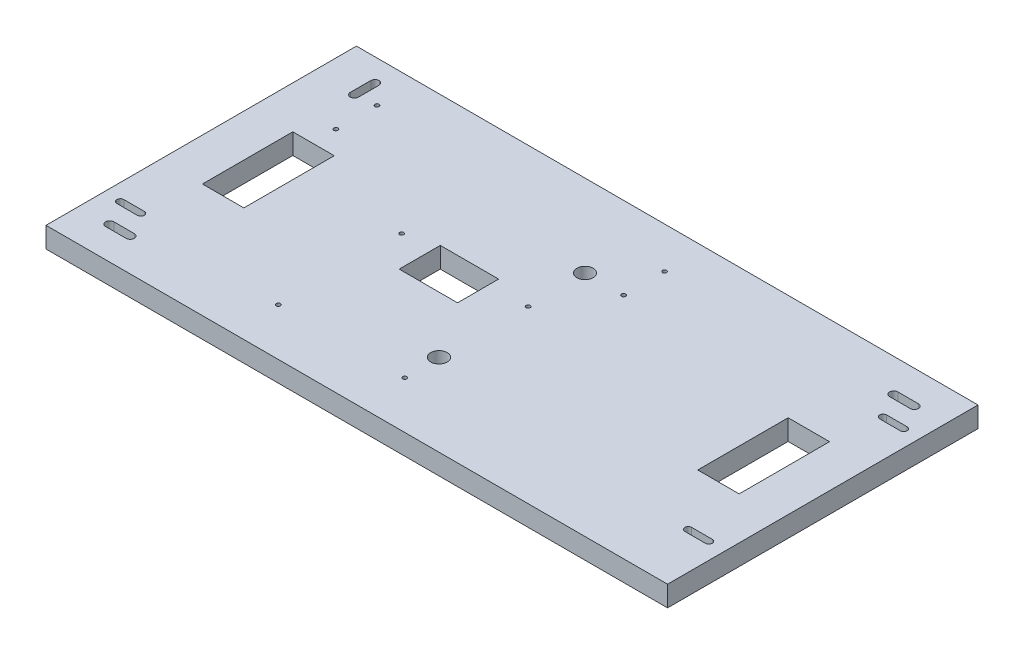
SolidWorks part; units mm, degrees
material "Corrugated Paper"
ref_plane "Front Plane" through (0, 0, 0) normal (0, 0, 1) x (1, 0, 0)
ref_plane "Top Plane" through (0, 0, 0) normal (0, 1, 0) x (1, 0, 0)
ref_plane "Right Plane" through (0, 0, 0) normal (1, 0, 0) x (0, 0, -1)
sketch "Sketch1" plane through (0, 0, 0) normal (0, 1, 0) x (1, 0, 0)
  line L1 (0, 0) -> (192.0875, 0)
  line L2 (0, 0) -> (0, 95.9358)
  line L3 (0, 95.9358) -> (192.0875, 95.9358)
  line L4 (192.0875, 0) -> (192.0875, 95.9358)
  dimension "D1" = 192.0875
  dimension "D2" = 95.9358
extrude "Boss-Extrude1" add sketch "Sketch1" along normal blind 6.35
sketch "Sketch3" plane through (0, 0, 0) normal (0, -1, 0) x (-1, 0, 0)
  line L0 (-12.7, 88.9508) -> (-12.7, 82.6008) construction
  line L1 (-11.43, 88.9508) -> (-11.43, 82.6008)
  line L2 (-13.97, 88.9508) -> (-13.97, 82.6008)
  line L3 (-192.0875, 95.9358) -> (0, 95.9358) construction
  line L4 (-5.1054, 17.8562) -> (-11.4554, 17.8562) construction
  line L5 (0, 95.9358) -> (0, 0) construction
  line L6 (0, 47.9679) -> (-192.0875, 47.9679) construction
  line L7 (-192.0875, 0) -> (-192.0875, 95.9358) construction
  line L8 (-96.0437, 0) -> (-96.0437, 95.9358) construction
  line L9 (0, 0) -> (-192.0875, 0) construction
  line L10 (-182.5625, 85.7758) -> (-176.2125, 85.7758) construction
  line L11 (-182.5625, 84.5058) -> (-176.2125, 84.5058)
  line L12 (-182.5625, 87.0458) -> (-176.2125, 87.0458)
  line L16 (-9.525, 10.16) -> (-15.875, 10.16) construction
  line L17 (-9.525, 11.43) -> (-15.875, 11.43)
  line L18 (-9.525, 8.89) -> (-15.875, 8.89)
  line L19 (-5.1054, 16.7894) -> (-11.4554, 16.7894)
  line L20 (-5.1054, 18.923) -> (-11.4554, 18.923)
  line L21 (-186.9821, 17.8562) -> (-180.6321, 17.8562) construction
  line L22 (-186.9821, 16.7894) -> (-180.6321, 16.7894)
  line L23 (-186.9821, 18.923) -> (-180.6321, 18.923)
  line L24 (-186.9821, 78.0796) -> (-180.6321, 78.0796) construction
  line L25 (-178.9811, 35.2298) -> (-178.9811, 63.1698)
  line L26 (-13.1064, 35.2298) -> (-25.908, 35.2298)
  line L27 (-13.1064, 35.2298) -> (-13.1064, 63.1698)
  line L28 (-13.1064, 63.1698) -> (-25.908, 63.1698)
  line L29 (-25.908, 35.2298) -> (-25.908, 63.1698)
  line L30 (-178.9811, 35.2298) -> (-166.1795, 35.2298)
  line L31 (-166.1795, 35.2298) -> (-166.1795, 63.1698)
  line L32 (-178.9811, 63.1698) -> (-166.1795, 63.1698)
  line L33 (-186.9821, 79.1464) -> (-180.6321, 79.1464)
  line L34 (-66.294, 42.8498) -> (-84.328, 42.8498)
  line L35 (-66.294, 42.8498) -> (-66.294, 55.5498)
  line L36 (-66.294, 55.5498) -> (-84.328, 55.5498)
  line L37 (-84.328, 42.8498) -> (-84.328, 55.5498)
  line L38 (-186.9821, 77.0128) -> (-180.6321, 77.0128)
  arc A0 (-11.43, 88.9508) -> (-13.97, 88.9508) centre (-12.7, 88.9508) ccw
  arc A1 (-13.97, 82.6008) -> (-11.43, 82.6008) centre (-12.7, 82.6008) ccw
  arc A2 (-182.5625, 84.5058) -> (-182.5625, 87.0458) centre (-182.5625, 85.7758) cw
  arc A3 (-176.2125, 87.0458) -> (-176.2125, 84.5058) centre (-176.2125, 85.7758) cw
  arc A6 (-9.525, 11.43) -> (-9.525, 8.89) centre (-9.525, 10.16) cw
  arc A7 (-15.875, 8.89) -> (-15.875, 11.43) centre (-15.875, 10.16) cw
  arc A8 (-5.1054, 16.7894) -> (-5.1054, 18.923) centre (-5.1054, 17.8562) ccw
  arc A9 (-11.4554, 18.923) -> (-11.4554, 16.7894) centre (-11.4554, 17.8562) ccw
  arc A10 (-186.9821, 16.7894) -> (-186.9821, 18.923) centre (-186.9821, 17.8562) cw
  arc A11 (-180.6321, 18.923) -> (-180.6321, 16.7894) centre (-180.6321, 17.8562) cw
  circle A12 centre (-96.0437, 25.4) radius 2.54
  circle A13 centre (-96.0437, 70.5358) radius 2.54
  arc A14 (-186.9821, 79.1464) -> (-186.9821, 77.0128) centre (-186.9821, 78.0796) ccw
  arc A15 (-180.6321, 77.0128) -> (-180.6321, 79.1464) centre (-180.6321, 78.0796) ccw
  point P2 (-12.7, 85.7758)
  point P21 (-179.3875, 85.7758)
  point P35 (-12.7, 10.16)
  point P42 (-8.2804, 17.8562)
  point P49 (-183.8071, 17.8562)
  point P72 (-183.8071, 78.0796)
  dimension "D21" = 5.08
  dimension "D3" = 12.7
  dimension "D4" = 10.16
  dimension "D5" = 6.35
  dimension "D6" = 2.1336
  dimension "D7" = 8.2804
  dimension "D8" = 17.8562
  dimension "D9" = 2.54
  dimension "D10" = 6.35
  dimension "D13" = 27.94
  dimension "D14" = 12.8016
  dimension "D15" = 32.766
  dimension "D16" = 25.908
  dimension "D17" = 12.7
  dimension "D18" = 18.034
  dimension "D19" = 66.294
  dimension "D20" = 40.386
  dimension "D22" = 25.4
sketch "Sketch8" plane through (0, -12.7, 0) normal (0, -1, 0) x (1, 0, 0)
  line L0 (0, -95.9358) -> (0, 0) construction
  line L2 (192.0875, -95.9358) -> (0, -95.9358) construction
  circle A0 centre (19.05, 5.6642) radius 0.635
  circle A1 centre (19.05, 18.3642) radius 0.635
  circle A2 centre (19.05, -70.5358) radius 0.635
  circle A3 centre (19.05, -83.2358) radius 0.635
  circle A4 centre (57.15, -52.7558) radius 0.635
  circle A5 centre (57.15, -14.6558) radius 0.635
  circle A6 centre (96.2406, -14.6558) radius 0.635
  circle A7 centre (96.2406, -52.7558) radius 0.635
  circle A8 centre (107.95, -83.2358) radius 0.635
  circle A9 centre (107.95, -70.5358) radius 0.635
  circle A10 centre (107.95, 5.6642) radius 0.635
  circle A11 centre (107.95, 18.3642) radius 0.635
  dimension "D1" = 1.27
  dimension "D3" = 1.27
  dimension "D5" = 1.27
  dimension "D6" = 1.27
  dimension "D13" = 1.27
  dimension "D14" = 1.27
  dimension "D15" = 1.27
  dimension "D21" = 1.27
  dimension "D25" = 1.27
  dimension "D28" = 1.27
  dimension "D31" = 1.27
  dimension "D34" = 1.27
  dimension "D2" = 19.05
  dimension "D4" = 12.7
  dimension "D7" = 19.05
  dimension "D8" = 19.05
  dimension "D9" = 12.7
  dimension "D10" = 12.7
  dimension "D11" = 76.2
  dimension "D12" = 19.05
  dimension "D16" = 38.1
  dimension "D17" = 57.15
  dimension "D18" = 43.18
  dimension "D19" = 57.15
  dimension "D20" = 39.0906
  dimension "D22" = 39.0906
  dimension "D23" = 38.1
  dimension "D24" = 43.18
  dimension "D26" = 12.7
  dimension "D27" = 88.9
  dimension "D29" = 12.7
  dimension "D30" = 88.9
  dimension "D32" = 88.9
  dimension "D33" = 76.2
  dimension "D35" = 12.7
  dimension "D36" = 88.9
extrude "Cut-Extrude2" cut sketch "Sketch8" against normal through all
extrude "Cut-Extrude3" cut sketch "Sketch3" against normal through all
